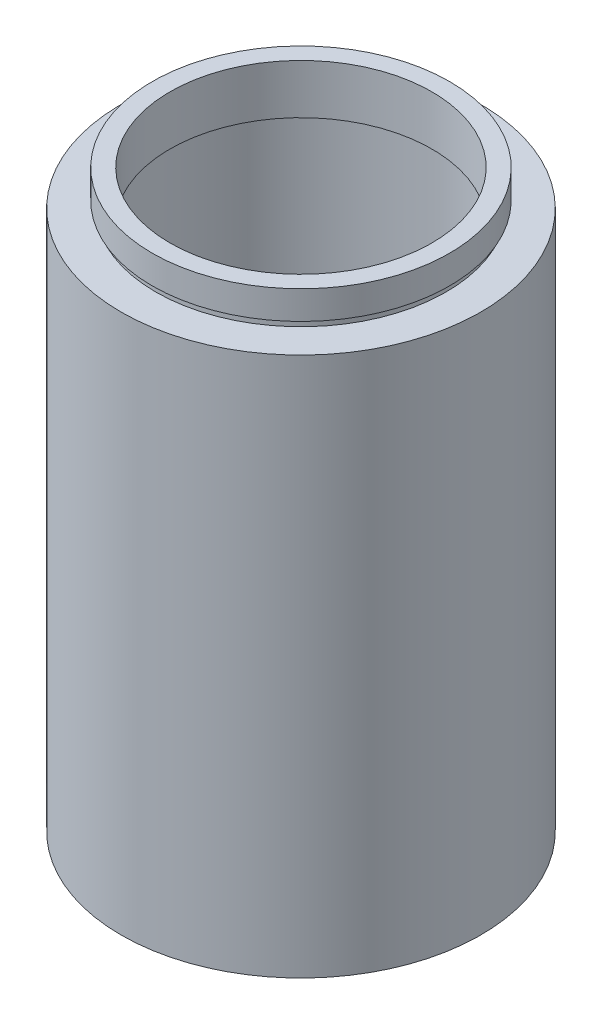
SolidWorks part; units mm, degrees
ref_plane "前视基准面" through (0, 0, 0) normal (0, 0, 1) x (1, 0, 0)
ref_plane "上视基准面" through (0, 0, 0) normal (0, 1, 0) x (1, 0, 0)
ref_plane "右视基准面" through (0, 0, 0) normal (1, 0, 0) x (0, 0, -1)
sketch "草图1" plane through (0, 0, 0) normal (0, 0, 1) x (1, 0, 0)
  line L0 (0, 161.3762) -> (0, 0) construction
  line L1 (141.7365, 0) -> (-131.7984, 0) construction
  line L2 (18.5, 81.2) -> (21, 81.2)
  line L3 (21, 81.2) -> (21, 77.2)
  line L4 (21, 77.2) -> (20.5, 77.2)
  line L5 (20.5, 77.2) -> (20.5, 76.2)
  line L6 (20.5, 76.2) -> (25.4, 76.2)
  line L7 (25.4, 76.2) -> (25.4, 0)
  line L8 (25.4, 0) -> (20.5, 0)
  line L9 (20.5, 0) -> (20.5, 73.2)
  line L10 (20.5, 73.2) -> (21.1, 73.2)
  line L11 (21.1, 73.2) -> (21.1, 74.2)
  line L12 (21.1, 74.2) -> (18.5, 74.2)
  line L13 (18.5, 74.2) -> (18.5, 81.2)
  dimension "D1" = 18.5
  dimension "D2" = 21
  dimension "D3" = 1
  dimension "D4" = 1
  dimension "D5" = 20.5
  dimension "D6" = 21.1
  dimension "D7" = 20.5
  dimension "D8" = 5
  dimension "D9" = 7
  dimension "D10" = 76.2
  dimension "D11" = 25.4
revolve "旋转1" add sketch "草图1" angle 360 about L0
cosmetic thread "装饰螺纹线1" parameters "D2"=42
cosmetic thread "装饰螺纹线2" parameters "D2"=38
cosmetic thread "装饰螺纹线3" parameters "D2"=41
